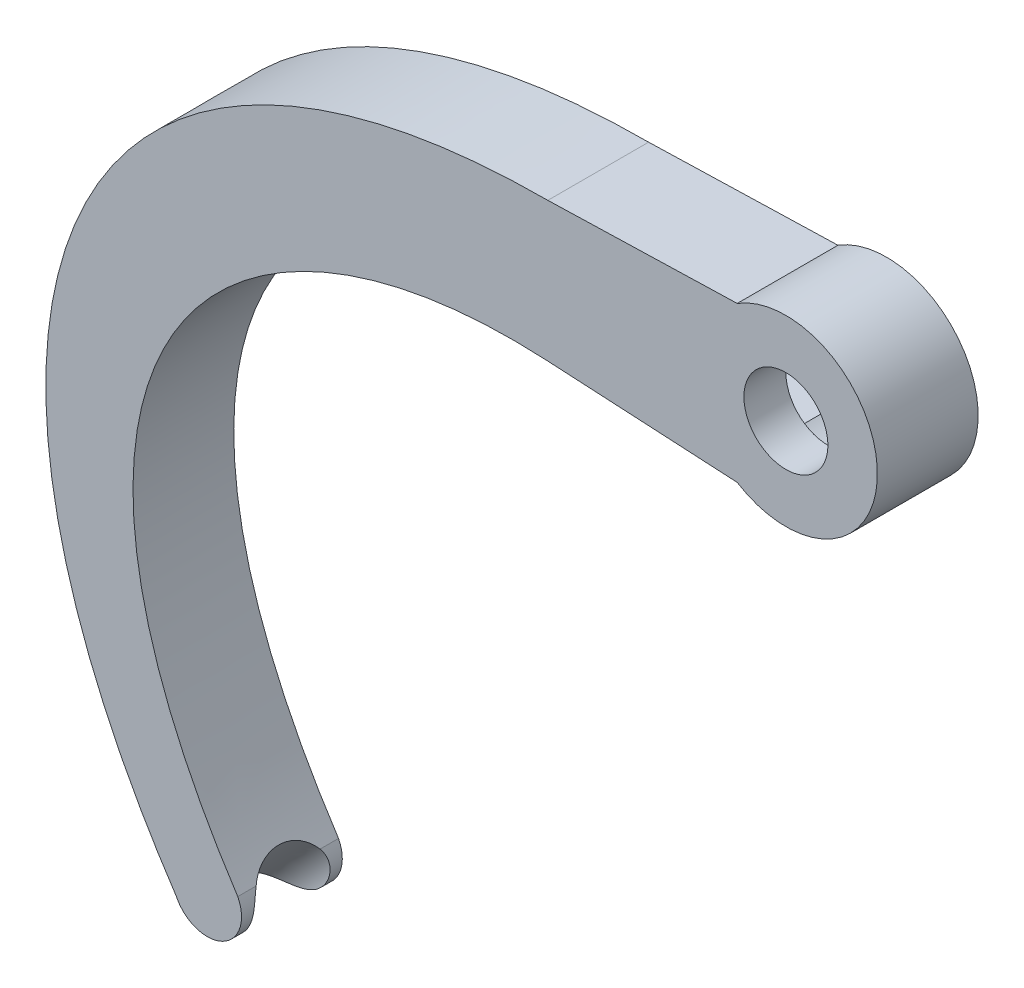
SolidWorks part; units mm, degrees
ref_plane "Front Plane" through (0, 0, 0) normal (0, 0, 1) x (1, 0, 0)
ref_plane "Top Plane" through (0, 0, 0) normal (0, 1, 0) x (1, 0, 0)
ref_plane "Right Plane" through (0, 0, 0) normal (1, 0, 0) x (0, 0, -1)
sketch "Sketch1" plane through (0, 0, 0) normal (0, 0, 1) x (1, 0, 0)
  line L0 (-14.2682, -3.994) -> (-34.7312, -2.8748) construction
  line L1 (-34.7312, -2.8748) -> (-47.0184, -18.9715) construction
  line L4 (0, 0) -> (0, 6)
  line L7 (-47.0184, -18.9715) -> (-32.6408, -40.8457) construction
  line L8 (-14.1753, 4.2925) -> (-42.4623, 4.2888) construction
  line L9 (-42.4623, 4.2888) -> (-52.5338, -18.3721) construction
  line L10 (-52.5338, -18.3721) -> (-36.3028, -42.6554) construction
  line L11 (-14.2095, -1.9943) -> (-2.2091, -2.65)
  line L12 (-2.2285, 2.6337) -> (-14.1644, 2.292)
  line L13 (-14.2682, -3.994) -> (-2.8985, -4.6153)
  line L14 (-2.8985, 4.6153) -> (-14.1753, 4.2925)
  arc A6 (-2.8985, -4.6153) -> (-2.8985, 4.6153) centre (0, 0) ccw
  arc A7 (-36.3028, -42.6554) -> (-32.6408, -40.8457) centre (-34.4578, -41.7789) ccw
  arc A8 (-14.1644, 2.292) -> (-14.2095, -1.9943) centre (-14.2218, 0.1492) ccw
  arc A9 (-2.2091, -2.65) -> (-2.2285, 2.6337) centre (0, 0) ccw
  arc A12 (-14.1753, 4.2925) -> (-14.2682, -3.994) centre (-14.2218, 0.1492) ccw construction
  spline S0 degree 3 poles (-14.2682, -3.994) (-34.7312, -2.8748) (-47.0184, -18.9715) (-32.6408, -40.8457) knots 0 0 0 0 1 1 1 1
  spline S1 degree 3 poles (-14.1753, 4.2925) (-42.4623, 4.2888) (-52.5338, -18.3721) (-36.3028, -42.6554) knots 0 0 0 0 1 1 1 1
  dimension "D1" = 6
  dimension "D2" = 2
extrude "Boss-Extrude1" add sketch "Sketch1" along normal blind 6 contours S1 A7 S0 L13 A6 L14
sketch "Sketch3" plane through (0, 0, 0) normal (0, 0, 1) x (1, 0, 0)
  line L9 (-14.1809, -2.3964) -> (-2.3593, -3.0424)
  line L10 (-2.3593, 3.0424) -> (-14.1809, 2.3964)
  arc A11 (-2.3593, -3.0424) -> (-2.3593, 3.0424) centre (0, 0) ccw
  arc A12 (-14.1809, 2.3964) -> (-14.1809, -2.3964) centre (-14.05, 0) ccw
extrude "Cut-Extrude1" cut sketch "Sketch3" along normal blind 3.5
sketch "Sketch4" plane through (0, 0, 3.5) normal (0, 0, -1) x (-1, 0, 0)
  circle A0 centre (0, 0) radius 2.5
  dimension "D1" = 5
extrude "Cut-Extrude2" cut sketch "Sketch4" against normal blind 3.5
ref_plane "Plane1" through (3.7258, 3.9776, 0) normal (0.6836, 0.7298, 0) x (0, 0, -1)
sketch "Sketch5" plane through (3.7258, 3.9776, 0) normal (0.6836, 0.7298, 0) x (0, 0, -1)
  line L0 (-6, -5.4554) -> (0, -5.4554) construction
  ellipse E0 centre (-3, -5.4554) end of major axis (-3, -7.8241) minor radius 2.322
ref_plane "Plane2" through (-23.6193, -25.2157, 0) normal (0.6836, 0.7298, 0) x (0, 0, -1)
sketch "Sketch6" plane through (-23.6193, -25.2157, 0) normal (0.6836, 0.7298, 0) x (0, 0, -1)
  ellipse E0 centre (-3, -5.4554) end of major axis (-3, -7.8241) minor radius 2.322 construction
  ellipse E1 centre (-3, -5.4554) end of major axis (-3, -7.8241) minor radius 2.322
extrude "Cut-Extrude3" cut sketch "Sketch6" against normal blind 30
